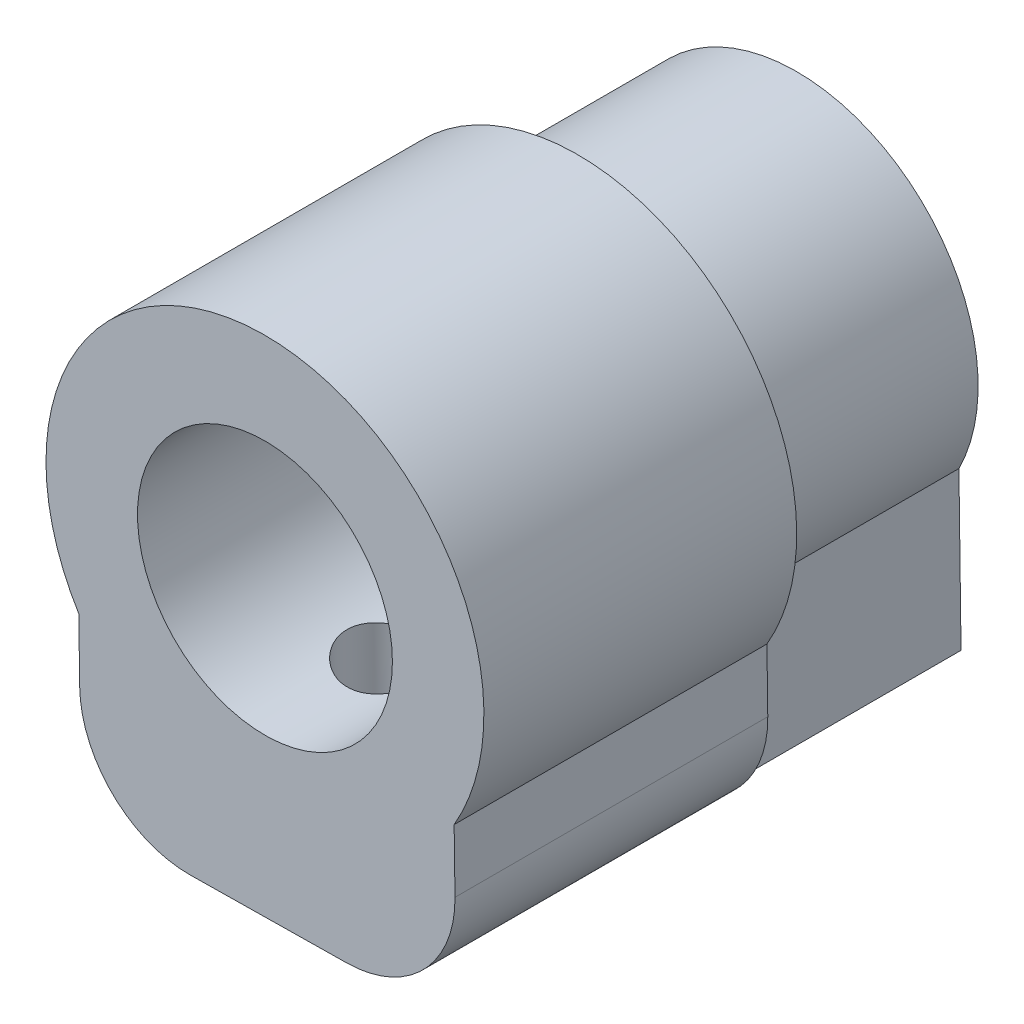
SolidWorks part; units mm, degrees
ref_plane "Front Plane" through (0, 0, 0) normal (0, 0, 1) x (1, 0, 0)
ref_plane "Top Plane" through (0, 0, 0) normal (0, 1, 0) x (1, 0, 0)
ref_plane "Right Plane" through (0, 0, 0) normal (1, 0, 0) x (0, 0, -1)
sketch "Sketch1" plane through (0, 0, 0) normal (0, 0, 1) x (1, 0, 0)
  line L0 (-5.2495, -4.7726) -> (5.0505, -4.6333)
  line L1 (-5.2495, -4.7726) -> (-5.1819, -9.7726)
  line L2 (5.0505, -4.6333) -> (5.1181, -9.6333)
  line L3 (-5.1819, -9.7726) -> (5.1181, -9.6333)
  circle A0 centre (-0.1356, -2.0362) radius 5.8
  dimension "D1" = 11.6
  dimension "D2" = 5.8
  dimension "D3" = 5.8
  dimension "D4" = 10.3
  dimension "D5" = 5
extrude "Boss-Extrude1" add sketch "Sketch1" along normal blind 7 contours A0 L1 L3 L2 | L0 A0 | L0 A0
sketch "Sketch2" plane through (0, 0, 7) normal (0, 0, 1) x (1, 0, 0)
  line L0 (5.9126, -5.5603) -> (-6.0863, -5.7226)
  line L1 (5.9126, -5.5603) -> (5.987, -11.0603)
  line L2 (-6.0863, -5.7226) -> (-6.0119, -11.2226)
  line L3 (5.987, -11.0603) -> (-6.0119, -11.2226)
  line L4 (-5.1819, -9.7726) -> (5.1181, -9.6333) construction
  circle A0 centre (-0.1356, -2.0362) radius 7
  arc A1 (5.0505, -4.6333) -> (-5.2495, -4.7726) centre (-0.1356, -2.0362) ccw construction
  circle A2 centre (-0.1356, -2.0362) radius 4.075
  line M1 (5.1181, -9.6333) -> (5.0505, -4.6333)
  arc M2 (5.0505, -4.6333) -> (-5.2495, -4.7726) centre (-0.1356, -2.0362) ccw
  line M3 (-5.2495, -4.7726) -> (-5.1819, -9.7726)
  line M4 (-5.1819, -9.7726) -> (5.1181, -9.6333)
  dimension "D1" = 0
  dimension "D2" = 14
  dimension "D3" = 0
  dimension "D4" = 8.15
  dimension "D5" = 7
  dimension "D6" = 7
  dimension "D7" = 12
  dimension "D8" = 180
  dimension "D9" = 5.5
extrude "Boss-Extrude3" add sketch "Sketch2" along normal blind 10 contours L0 A0 M3 M2 M1 | A2 L0 M1 M2 M3 | A2 L0 A0 M3 M1 | A0 M3 M4 M1 | A0 L2 L3 L1 M1 M4 M3 | A0 L0 M1 | L0 A0 M3
sketch "Sketch6" plane through (0.1507, -11.1392, 0) normal (0.0135, -0.9999, 0) x (-0.9999, -0.0135, 0)
  line L0 (-5.8369, -17) -> (6.1631, -17) construction
  circle A0 centre (0.2412, -13) radius 1.35
  point P2 (0.1631, -17)
  dimension "D2" = 2.7
  dimension "D1" = 4
extrude "Cut-Extrude3" cut sketch "Sketch6" against normal blind 12
fillet "Fillet1" radius 3.5 1 edges at (5.987, -11.0603, 12)
fillet "Fillet2" radius 3.5 1 edges at (-6.0119, -11.2226, 12)
